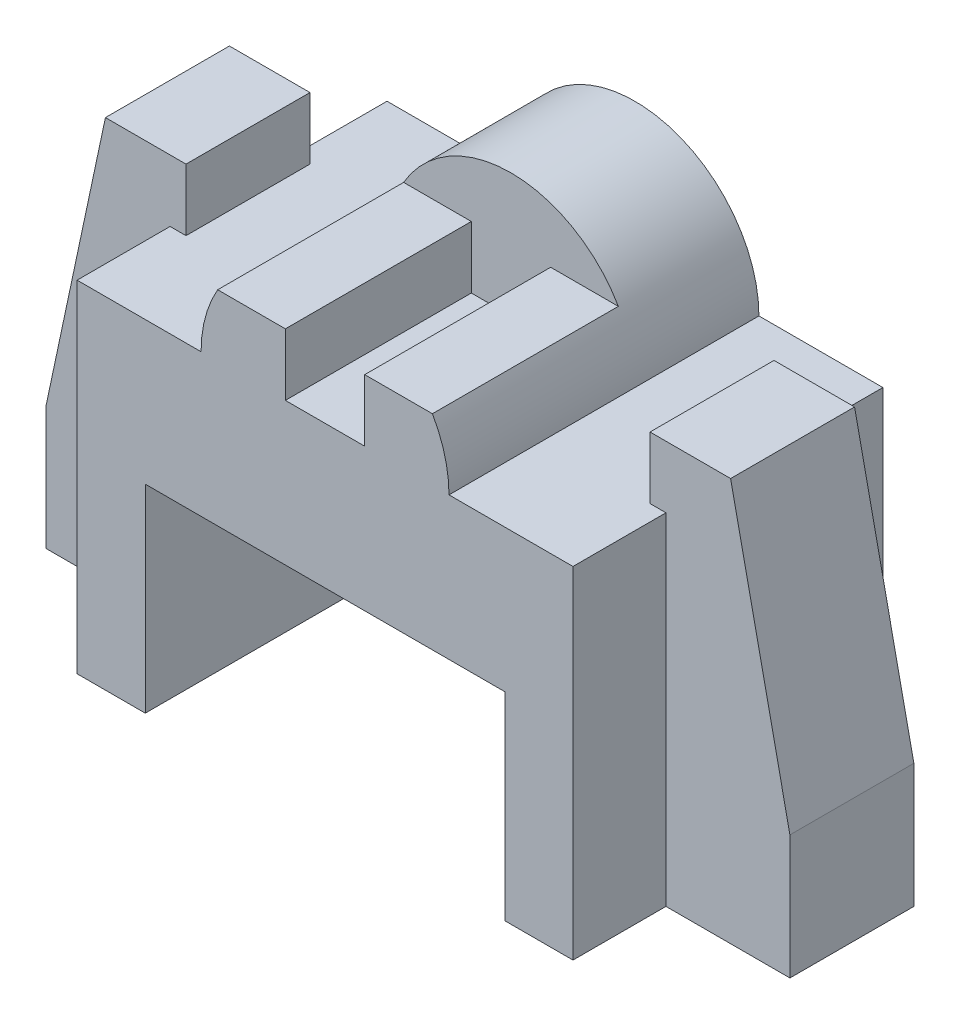
SolidWorks part; units mm, degrees
ref_plane "Front Plane" through (0, 0, 0) normal (0, 0, 1) x (1, 0, 0)
ref_plane "Top Plane" through (0, 0, 0) normal (0, 1, 0) x (1, 0, 0)
ref_plane "Right Plane" through (0, 0, 0) normal (1, 0, 0) x (0, 0, -1)
sketch "Sketch1" plane through (0, 0, 0) normal (0, 0, 1) x (1, 0, 0)
  line L0 (0, 0) -> (11, 0)
  line L2 (0, 0) -> (0, 55)
  line L3 (0, 55) -> (80, 55)
  line L4 (80, 0) -> (80, 55)
  line L5 (11, 0) -> (11, 32)
  line L6 (11, 32) -> (69, 32)
  line L7 (69, 32) -> (69, 0)
  line L9 (69, 0) -> (80, 0)
  dimension "D1" = 11
  dimension "D2" = 69
  dimension "D3" = 32
  dimension "D4" = 55
extrude "Boss-Extrude1" add sketch "Sketch1" against normal blind 50 contours L6 L7 L9 L4 L3 L2 L0 L5
sketch "Sketch2" plane through (0, 0, 0) normal (0, 0, 1) x (1, 0, 0)
  line L0 (0, 0) -> (-20, 0)
  line L1 (-20, 0) -> (-20, 20)
  line L4 (2.57, 55) -> (2.57, 65)
  line L5 (2.57, 65) -> (-10.43, 65)
  line L6 (-10.43, 65) -> (-20, 20)
  line L7 (0, 0) -> (0, 55)
  line L8 (0, 0) -> (0, 55) construction
  line L9 (0, 55) -> (80, 55) construction
  line L10 (0, 55) -> (2.57, 55)
  line L13 (80, 0) -> (100, 0)
  line L14 (100, 0) -> (100, 20)
  line L15 (90.43, 65) -> (100, 20)
  line L16 (77.43, 65) -> (90.43, 65)
  line L17 (77.43, 55) -> (77.43, 65)
  line L18 (80, 55) -> (77.43, 55)
  line L19 (80, 0) -> (80, 55)
  dimension "D1" = 2.57
  dimension "D2" = 77.43
  dimension "D3" = 90.43
  dimension "D4" = 100
  dimension "D5" = 65
extrude "Boss-Extrude2" add sketch "Sketch2" against normal blind 35 and the other way through all
sketch "Sketch3" plane through (0, 0, 0) normal (0, 0, 1) x (1, 0, 0)
  line L7 (0, 0) -> (0, 55)
  line L8 (0, 55) -> (2.57, 55)
  line L9 (2.57, 55) -> (2.57, 65)
  line L10 (2.57, 65) -> (-10.43, 65)
  line L11 (-10.43, 65) -> (-20, 20)
  line L12 (-20, 20) -> (-20, 0)
  line L13 (-20, 0) -> (0, 0)
  line L14 (0, 0) -> (0, 55)
  line L15 (0, 55) -> (2.57, 55)
  line L16 (2.57, 55) -> (2.57, 65)
  line L17 (2.57, 65) -> (-10.43, 65)
  line L18 (-10.43, 65) -> (-20, 20)
  line L19 (-20, 20) -> (-20, 0)
  line L20 (-20, 0) -> (0, 0)
  dimension "D1" = 0
extrude "Cut-Extrude1" cut sketch "Sketch3" against normal blind 15
sketch "Sketch4" plane through (0, 0, 0) normal (0, 0, 1) x (1, 0, 0)
  line L9 (80, 55) -> (80, 0)
  line L10 (80, 0) -> (100, 0)
  line L11 (100, 0) -> (100, 20)
  line L12 (100, 20) -> (90.43, 65)
  line L13 (90.43, 65) -> (77.43, 65)
  line L14 (77.43, 65) -> (77.43, 55)
  line L15 (77.43, 55) -> (80, 55)
  line L16 (80, 55) -> (80, 0)
  line L17 (80, 0) -> (100, 0)
  line L18 (100, 0) -> (100, 20)
  line L19 (100, 20) -> (90.43, 65)
  line L20 (90.43, 65) -> (77.43, 65)
  line L21 (77.43, 65) -> (77.43, 55)
  line L22 (77.43, 55) -> (80, 55)
  dimension "D1" = 0
extrude "Cut-Extrude2" cut sketch "Sketch4" against normal blind 15
sketch "Sketch6" plane through (0, 0, 0) normal (0, 0, 1) x (1, 0, 0)
  line L0 (0, 55) -> (80, 55) construction
  circle A0 centre (40, 55) radius 20
  dimension "D1" = 40
extrude "Boss-Extrude3" add sketch "Sketch6" against normal blind 50
sketch "Sketch8" plane through (0, 0, 0) normal (0, 0, 1) x (1, 0, 0)
  line L0 (20, 55) -> (60, 55)
  arc A0 (60, 55) -> (20, 55) centre (40, 55) ccw
  dimension "D1" = 20
sketch "Sketch9" plane through (0, 0, 0) normal (0, 0, 1) x (1, 0, 0)
  line L0 (20, 55) -> (33.6, 55)
  line L1 (20, 55) -> (60, 55) construction
  line L2 (60, 55) -> (46.4, 55)
  line L3 (46.4, 55) -> (46.4, 65)
  line L4 (46.4, 65) -> (57.3205, 65)
  line L5 (33.6, 55) -> (33.6, 65)
  line L6 (33.6, 65) -> (22.6795, 65)
  line L7 (0, 0) -> (0, 55) construction
  arc A0 (60, 55) -> (20, 55) centre (40, 55) ccw construction
  arc A1 (60, 55) -> (57.3205, 65) centre (40, 55) ccw
  arc A2 (22.6795, 65) -> (20, 55) centre (40, 55) ccw
  dimension "D1" = 22.6795
  dimension "D2" = 33.6
extrude "Cut-Extrude4" cut sketch "Sketch8" against normal blind 30
extrude "Boss-Extrude4" add sketch "Sketch9" against normal blind 30
